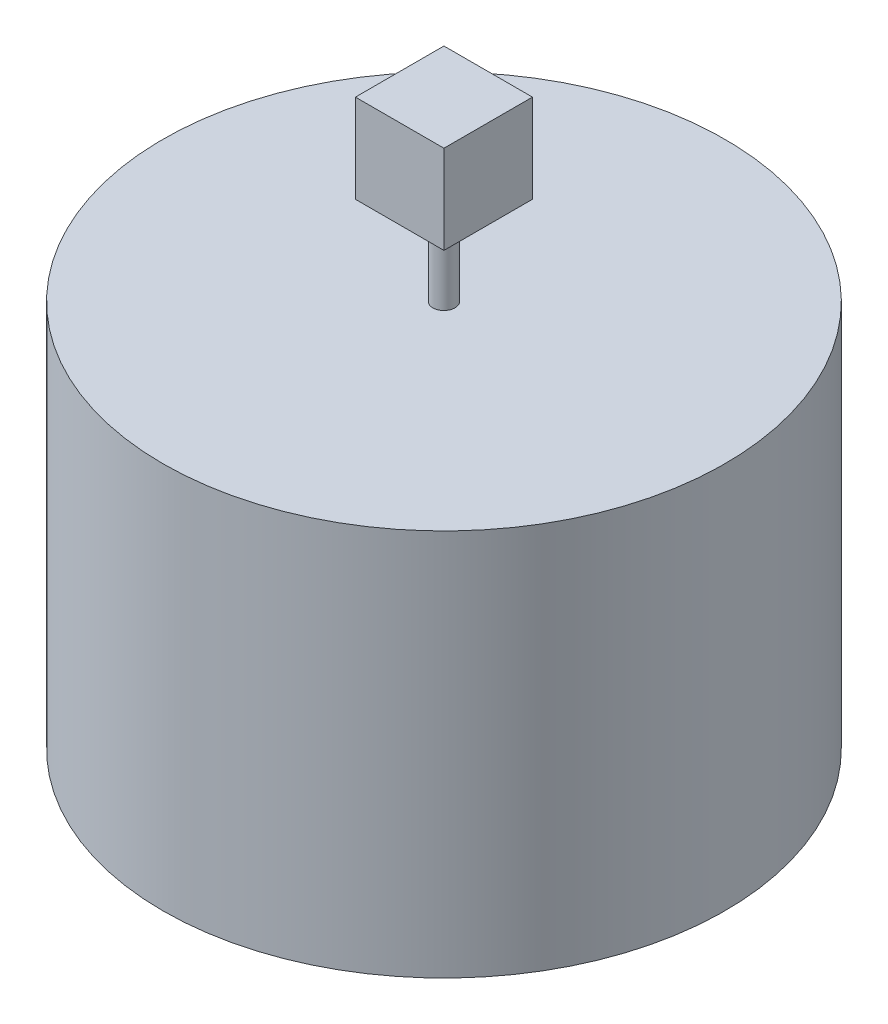
SolidWorks part; units mm, degrees
ref_plane "Plan de face" through (0, 0, 0) normal (0, 0, 1) x (1, 0, 0)
ref_plane "Plan de dessus" through (0, 0, 0) normal (0, 1, 0) x (1, 0, 0)
ref_plane "Plan de droite" through (0, 0, 0) normal (1, 0, 0) x (0, 0, -1)
sketch "Esquisse1" plane through (0, 0, 0) normal (0, 1, 0) x (1, 0, 0)
  circle A0 centre (0, 0) radius 254
  dimension "D1" = 508
extrude "Extrusion1" add sketch "Esquisse1" along normal blind 350
sketch "Esquisse2" plane through (0, 350, 0) normal (0, 1, 0) x (1, 0, 0)
  circle A0 centre (0, 0) radius 10
  dimension "D1" = 20
extrude "Extrusion2" add sketch "Esquisse2" along normal blind 80
sketch "Esquisse3" plane through (0, 430, 0) normal (0, 1, 0) x (1, 0, 0)
  line L0 (0, -10) -> (0, 40) construction
  line L1 (-10, 0) -> (40, 0) construction
  line L3 (-40, -40) -> (40, -40)
  line L4 (-40, -40) -> (-40, 40)
  line L5 (-40, 40) -> (40, 40)
  line L6 (40, -40) -> (40, 40)
  circle A0 centre (0, 0) radius 10 construction
  dimension "D1" = 80
extrude "Extrusion3" add sketch "Esquisse3" along normal blind 80
